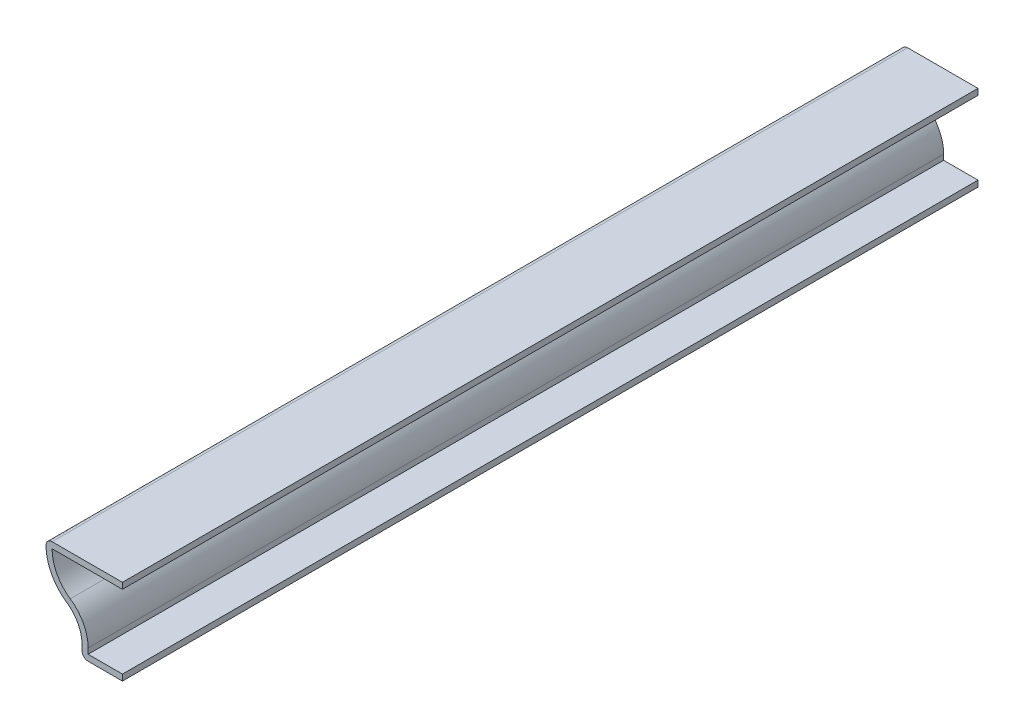
SolidWorks part; units mm, degrees
ref_plane "Front Plane" through (0, 0, 0) normal (0, 0, 1) x (1, 0, 0)
ref_plane "Top Plane" through (0, 0, 0) normal (0, 1, 0) x (1, 0, 0)
ref_plane "Right Plane" through (0, 0, 0) normal (1, 0, 0) x (0, 0, -1)
sketch "Sketch1" plane through (0, 0, 0) normal (0, 0, 1) x (1, 0, 0)
  line L0 (0, 0) -> (0, 18.9035) construction
  line L1 (0, 0) -> (-6.7469, 0)
  line L2 (-12.7, 14.2875) -> (0, 14.2875)
  line L3 (-6.7469, 0) -> (-6.7469, 1.9191)
  arc A0 (-6.7469, 1.9191) -> (-9.2824, 6.7019) centre (-12.5254, 1.9191) ccw
  arc A1 (-9.2824, 6.7019) -> (-12.7, 14.2875) centre (-4.8278, 13.2715) cw
  point P10 (0, 0)
  dimension "D3" = 7.9375
  dimension "D4" = 5.7785
  dimension "D1" = 14.2875
  dimension "D2" = 1.016
  dimension "D5" = 6.7469
  dimension "D6" = 12.7
extrude "Extrude-Thin1" add sketch "Sketch1" against normal blind 142.875 thin
fillet "Fillet1" radius 1.016 2 edges at (-12.7, 14.2875, -71.4375) (-6.7469, 0, -71.4375)
